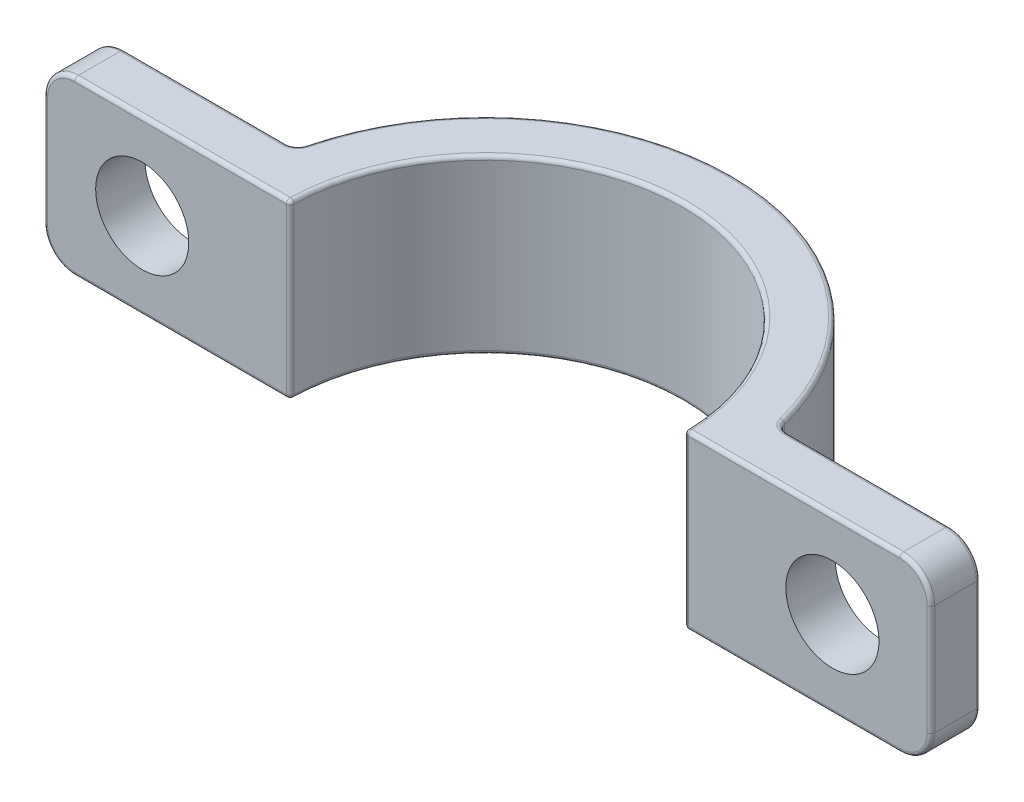
SolidWorks part; units mm, degrees
material "7075-T6 (SN)"
ref_plane "Płaszczyzna XY" through (0, 0, 0) normal (0, 0, 1) x (1, 0, 0)
ref_plane "Płaszczyzna XZ" through (0, 0, 0) normal (0, 1, 0) x (1, 0, 0)
ref_plane "Płaszczyzna YZ" through (0, 0, 0) normal (1, 0, 0) x (0, 0, -1)
sketch "Szkic1" plane through (0, 0, 0) normal (0, 1, 0) x (1, 0, 0)
  line L0 (0, 0) -> (0, 9.7155) construction
  line L1 (-28.575, 0.1137) -> (-12.6995, 0.1137)
  line L2 (-28.575, 0.1137) -> (-28.575, 3.2937)
  line L3 (-28.575, 3.2937) -> (-15.5347, 3.2937)
  line L4 (28.575, 0.1137) -> (28.575, 3.2937)
  line L5 (15.5347, 3.2937) -> (28.575, 3.2937)
  line L6 (12.6995, 0.1137) -> (28.575, 0.1137)
  arc A0 (15.5347, 3.2937) -> (-15.5347, 3.2937) centre (0, 0) ccw
  arc A1 (12.6995, 0.1137) -> (-12.6995, 0.1137) centre (0, 0) ccw
  point P8 (28.575, 1.7037)
  dimension "D1" = 3.18
  dimension "D4" = 12.7
  dimension "D5" = 15.88
  dimension "D2" = 57.15
  dimension "D3" = 15.8755
extrude "Dodanie-wyciągnięcie1" add sketch "Szkic1" along normal blind 11.11 contours A1 L1 L2 L3 A0 L5 L4 L6
sketch "Szkic2" plane through (0, 0, -3.2937) normal (0, 0, -1) x (-1, 0, 0)
  line L0 (22.23, 5.56) -> (-22.23, 5.56)
  line L1 (-15.5347, 0) -> (-28.575, 0) construction
  line L2 (0, 0) -> (0, 11.11) construction
  line L3 (15.5347, 11.11) -> (-15.5347, 11.11) construction
  dimension "D1" = 5.56
  dimension "D2" = 22.23
  dimension "D3" = 22.23
hole_wizard "Otwory ustalające Ø6.0mm1" positions "Szkic3" profile "Szkic4" hole size "Ø6.0" standard "ISO" end condition up to next
sketch "Szkic3" plane through (0, 0, -3.2937) normal (0, 0, -1) x (-1, 0, 0)
  point P0 (-22.23, 5.56)
  point P3 (22.23, 5.56)
sketch "Szkic4" plane through (22.23, 5.56, -3.2937) normal (1, 0, 0) x (0, 1, 0)
  line L0 (0, 0) -> (0, 3.18)
  line L1 (0, 3.18) -> (3, 3.18)
  line L2 (3, 3.18) -> (3, 0)
  line L5 (3, 0) -> (0, 0)
  line L11 (0, -6.35) -> (0, 107.95) construction
  dimension "Średnica otworu na wylot" = 6
  dimension "Głębokość otworu na wylot" = 3.18
fillet "Zaokrąglenie1" radius 2 4 edges at (28.575, 0, -1.7037) (28.575, 11.11, -1.7037) (-28.575, 11.11, -1.7037) (-28.575, 0, -1.7037)
fillet "Zaokrąglenie2" radius 0.76 2 edges at (-15.5347, 5.555, -3.2937) (15.5347, 5.555, -3.2937)
fillet "Zaokrąglenie4" radius 0.25 30 edges at (15.6713, 0, -3.4544) (21.3568, 0, -3.2937) (27.9892, 0.5858, -3.2937) (28.575, 5.555, -3.2937) (27.9892, 10.5242, -3.2937) (21.3568, 11.11, -3.2937) (15.6713, 11.11, -3.4544) (0, 11.11, -15.88) (-15.6713, 11.11, -3.4544) (-21.3568, 11.11, -3.2937) (-27.9892, 10.5242, -3.2937) (-28.575, 5.555, -3.2937) (-27.9892, 0.5858, -3.2937) (-21.3568, 0, -3.2937) (-15.6713, 0, -3.4544) (0, 0, -15.88) (-19.6372, 0, -0.1137) (-27.9892, 0.5858, -0.1137) (-28.575, 5.555, -0.1137) (-27.9892, 10.5242, -0.1137) (19.6372, 0, -0.1137) (27.9892, 0.5858, -0.1137) (28.575, 5.555, -0.1137) (27.9892, 10.5242, -0.1137) (12.6995, 5.555, -0.1137) (-12.6995, 5.555, -0.1137) (0, 0, -12.7) (-19.6372, 11.11, -0.1137) (19.6372, 11.11, -0.1137) (0, 11.11, -12.7)
